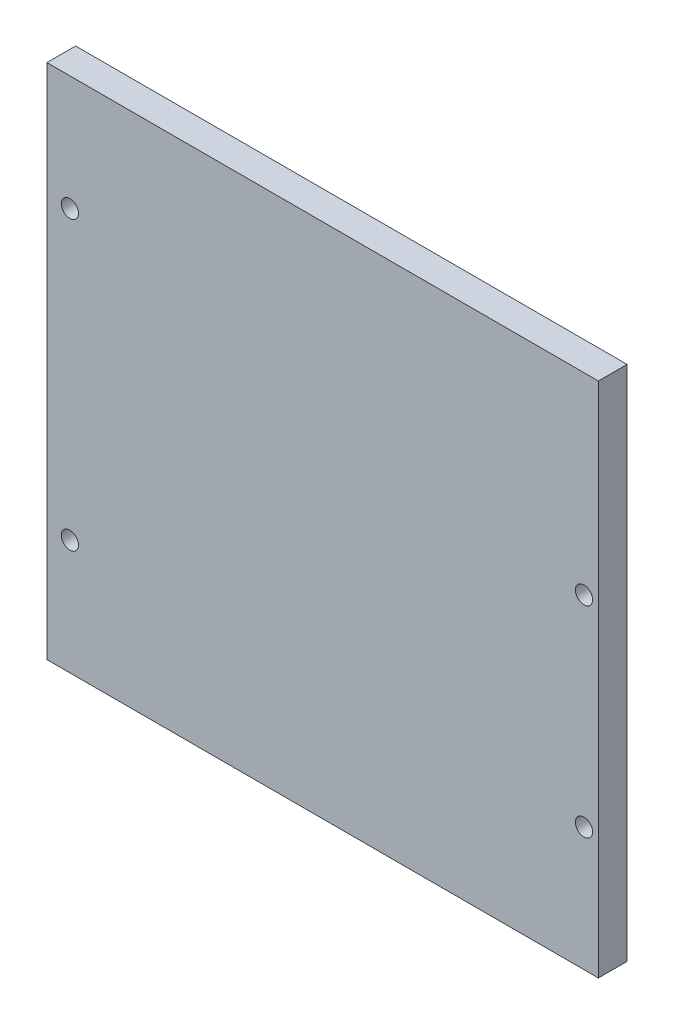
SolidWorks part; units mm, degrees
ref_plane "Front Plane" through (0, 0, 0) normal (0, 0, 1) x (1, 0, 0)
ref_plane "Top Plane" through (0, 0, 0) normal (0, 1, 0) x (1, 0, 0)
ref_plane "Right Plane" through (0, 0, 0) normal (1, 0, 0) x (0, 0, -1)
sketch "Sketch1" plane through (0, 0, 0) normal (0, 0, 1) x (1, 0, 0)
  line L1 (-48, 45) -> (48, 45)
  line L2 (-48, 45) -> (-48, -45)
  line L3 (-48, -45) -> (48, -45)
  line L4 (48, 45) -> (48, -45)
  line L5 (-48, 45) -> (48, -45) construction
  line L6 (-48, -45) -> (48, 45) construction
  point P0 (0, 0)
  dimension "D1" = 90
  dimension "D2" = 96
extrude "Boss-Extrude1" add sketch "Sketch1" along normal blind 5
sketch "Sketch2" plane through (0, 0, 5) normal (0, 0, 1) x (1, 0, 0)
  line L0 (45.5, 11.5) -> (45.5, -23.5) construction
  line L3 (48, -45) -> (48, 45) construction
  line L4 (-48, -45) -> (48, -45) construction
  circle A0 centre (45.5, 11.5) radius 1.5
  circle A1 centre (45.5, -23.5) radius 1.5
  dimension "D3" = 3
  dimension "D2" = 21.5
  dimension "D1" = 35
  dimension "D4" = 2.5
extrude "Cut-Extrude1" cut sketch "Sketch2" against normal through all
sketch "Sketch3" plane through (0, 0, 5) normal (0, 0, 1) x (1, 0, 0)
  line L0 (-44, 25) -> (-44, -25) construction
  line L1 (0, 0) -> (-44, 0) construction
  line L2 (-48, 45) -> (-48, -45) construction
  circle A0 centre (-44, 25) radius 1.5
  circle A1 centre (-44, -25) radius 1.5
  dimension "D2" = 3
  dimension "D1" = 50
  dimension "D3" = 4
extrude "Cut-Extrude2" cut sketch "Sketch3" against normal through all
sketch "草图1" plane through (0, 0, 5) normal (0, 0, 1) x (1, 0, 0)
  line L0 (-78, 75) -> (-78, -75)
  line L1 (-48, 45) -> (48, 45)
  line L2 (-48, 45) -> (-48, -45)
  line L3 (-48, -45) -> (48, -45)
  line L4 (48, 45) -> (48, -45)
  line L5 (-78, -75) -> (78, -75)
  line L6 (78, 75) -> (78, -75)
  line L7 (-78, 75) -> (78, 75)
  dimension "D1" = 30
